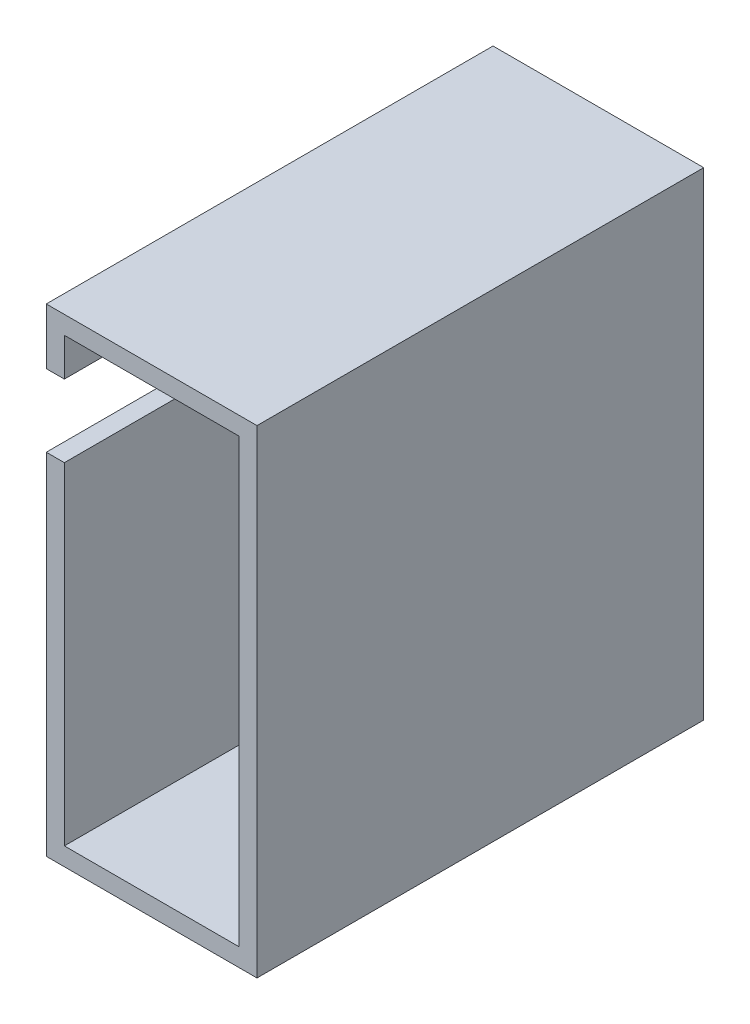
SolidWorks part; units mm, degrees
ref_plane "Front Plane" through (0, 0, 0) normal (0, 0, 1) x (1, 0, 0)
ref_plane "Top Plane" through (0, 0, 0) normal (0, 1, 0) x (1, 0, 0)
ref_plane "Right Plane" through (0, 0, 0) normal (1, 0, 0) x (0, 0, -1)
sketch "Sketch1" plane through (0, 0, 0) normal (0, 0, 1) x (1, 0, 0)
  line L1 (0, 0) -> (19.3, 0)
  line L2 (0, 0) -> (0, 48.9)
  line L3 (0, 48.9) -> (19.3, 48.9)
  line L4 (19.3, 0) -> (19.3, 48.9)
  line L5 (0, 0) -> (19.3, 48.9) construction
  line L6 (0, 48.9) -> (19.3, 0) construction
  line L7 (-2, 50.9) -> (21.3, 50.9)
  line L8 (-2, 50.9) -> (-2, -2)
  line L9 (-2, -2) -> (21.3, -2)
  line L10 (21.3, 50.9) -> (21.3, -2)
  line L11 (-2, 50.9) -> (21.3, -2) construction
  line L12 (-2, -2) -> (21.3, 50.9) construction
  point P4 (9.65, 24.45)
  point P10 (9.65, 24.45)
  dimension "D1" = 19.3
  dimension "D2" = 48.9
  dimension "D3" = 2
  dimension "D4" = 2
  dimension "D5" = 2
  dimension "D6" = 2
extrude "Boss-Extrude1" add sketch "Sketch1" along normal blind 47.4 contours L10 L7 L8 L9 L4 L1 L2 L3
sketch "Sketch2" plane through (0, 0, 0) normal (0, 0, -1) x (-1, 0, 0)
  line L8 (-21.3, 50.9) -> (-21.3, -2)
  line L9 (-21.3, -2) -> (2, -2)
  line L10 (2, -2) -> (2, 50.9)
  line L11 (2, 50.9) -> (-21.3, 50.9)
  line L12 (-21.3, 50.9) -> (-21.3, -2)
  line L13 (-21.3, -2) -> (2, -2)
  line L14 (2, -2) -> (2, 50.9)
  line L15 (2, 50.9) -> (-21.3, 50.9)
  dimension "D1" = 0
extrude "Boss-Extrude2" add sketch "Sketch2" along normal blind 2
sketch "Sketch3" plane through (-2, 0, 0) normal (-1, 0, 0) x (0, 0, 1)
  line L0 (3, 50.9) -> (3, 40.7) construction
  line L1 (47.4, 50.9) -> (-2, 50.9) construction
  line L2 (3, 40.7) -> (47.4, 40.7) construction
  line L3 (3, 44.7) -> (47.4, 44.7)
  line L4 (3, 36.7) -> (47.4, 36.7)
  line L5 (47.4, 50.9) -> (47.4, -2) construction
  line L6 (-2, -2) -> (-2, 50.9) construction
  arc A0 (3, 44.7) -> (3, 36.7) centre (3, 40.7) ccw
  arc A1 (47.4, 36.7) -> (47.4, 44.7) centre (47.4, 40.7) ccw
  point P4 (25.2, 40.7)
  point P10 (47.4, 40.7)
  point P13 (1.1055, 40.7)
  dimension "D1" = 10.2
  dimension "D2" = 5
  dimension "D3" = 8
extrude "Cut-Extrude1" cut sketch "Sketch3" against normal blind 2
